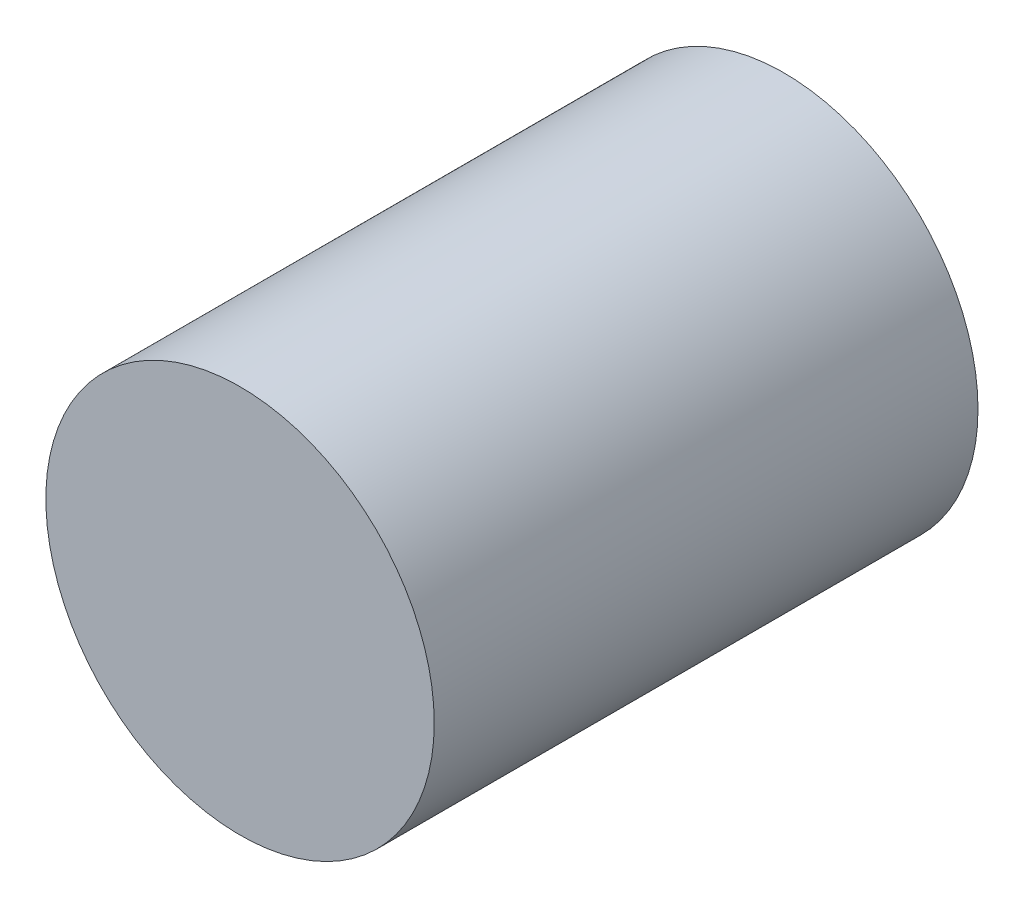
SolidWorks part; units mm, degrees
ref_plane "Front Plane" through (0, 0, 0) normal (0, 0, 1) x (1, 0, 0)
ref_plane "Top Plane" through (0, 0, 0) normal (0, 1, 0) x (1, 0, 0)
ref_plane "Right Plane" through (0, 0, 0) normal (1, 0, 0) x (0, 0, -1)
sketch "Sketch1" plane through (0, 0, 0) normal (0, 0, 1) x (1, 0, 0)
  circle A0 centre (0, 0) radius 50
  dimension "D1" = 100
extrude "Boss-Extrude1" add sketch "Sketch1" along normal blind 140
sketch "Sketch4" plane through (0, 0, 0) normal (0, 0, -1) x (-1, 0, 0)
  circle A0 centre (0, 0) radius 30
  dimension "D1" = 60
extrude "Cut-Extrude1" cut sketch "Sketch4" against normal blind 40
sketch "Sketch5" plane through (0, 0, 0) normal (0, 0, -1) x (-1, 0, 0)
  circle A0 centre (0, 0) radius 10
  dimension "D1" = 20
extrude "Cut-Extrude2" cut sketch "Sketch5" against normal blind 120
